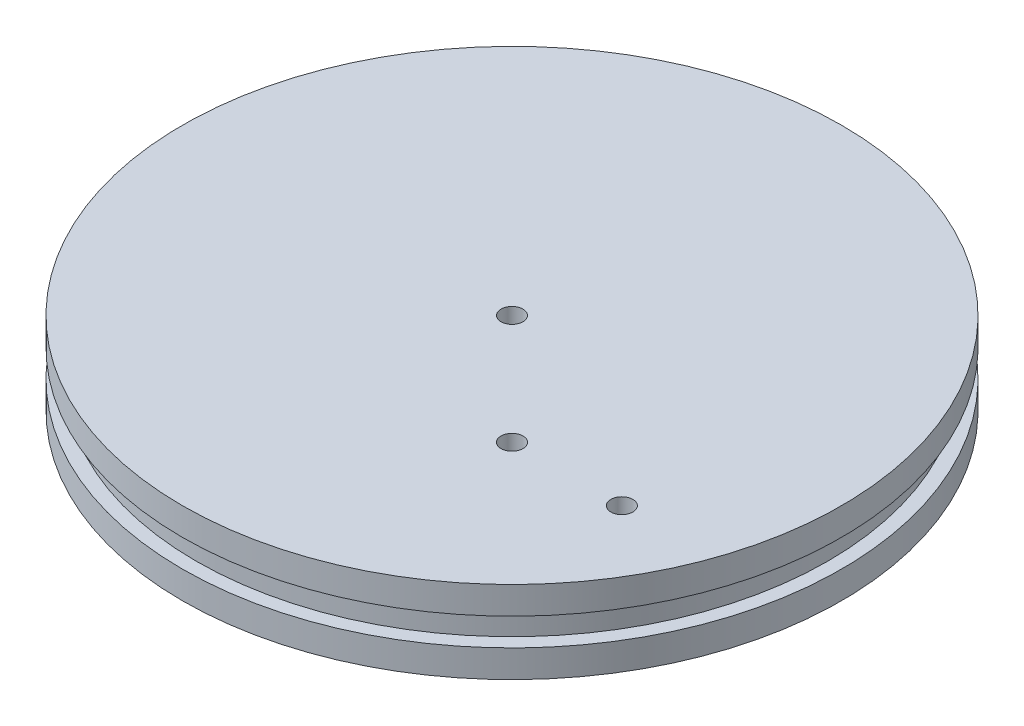
SolidWorks part; units mm, degrees
ref_plane "Front Plane" through (0, 0, 0) normal (0, 0, 1) x (1, 0, 0)
ref_plane "Top Plane" through (0, 0, 0) normal (0, 1, 0) x (1, 0, 0)
ref_plane "Right Plane" through (0, 0, 0) normal (1, 0, 0) x (0, 0, -1)
sketch "Sketch1" plane through (0, 0, 0) normal (0, 1, 0) x (1, 0, 0)
  line L0 (25.4, -25.4) -> (50.8, -25.4) construction
  circle A0 centre (0, 0) radius 76.2
  circle A1 centre (0, 0) radius 2.54
  circle A2 centre (25.4, -25.4) radius 2.54
  circle A3 centre (50.8, -25.4) radius 2.54
  dimension "D1" = 5.08
  dimension "D2" = 152.4
  dimension "D3" = 25.4
  dimension "D4" = 50.8
  dimension "D5" = 25.4
extrude "Boss-Extrude1" add sketch "Sketch1" along normal blind 19.05
sketch "Sketch2" plane through (0, 0, 0) normal (0, 0, 1) x (1, 0, 0)
  line L1 (-76.2, 12.7) -> (-73.025, 12.7)
  line L2 (-76.2, 12.7) -> (-76.2, 6.35)
  line L3 (-76.2, 6.35) -> (-73.025, 6.35)
  line L4 (-73.025, 12.7) -> (-73.025, 6.35)
  line L5 (-76.2, 19.05) -> (-76.2, 0) construction
  line L6 (-73.025, 9.525) -> (-76.2, 9.525) construction
  line L8 (0, 4.7625) -> (0, 26.7643) construction
  line L9 (0, 4.7625) -> (0, -3.97) construction
  dimension "D1" = 6.35
  dimension "D2" = 3.175
revolve "Cut-Revolve1" cut sketch "Sketch2" angle 360 about L8
